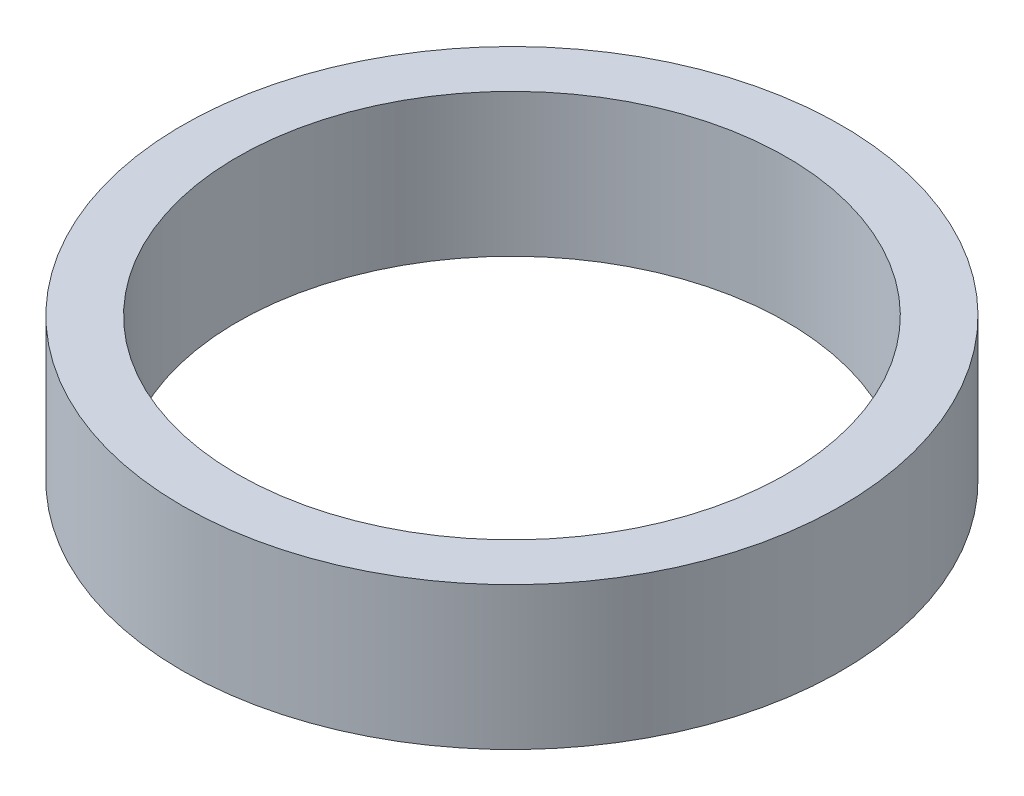
SolidWorks part; units mm, degrees
material "AISI 304"
ref_plane "前视基准面" through (0, 0, 0) normal (0, 0, 1) x (1, 0, 0)
ref_plane "上视基准面" through (0, 0, 0) normal (0, 1, 0) x (1, 0, 0)
ref_plane "右视基准面" through (0, 0, 0) normal (1, 0, 0) x (0, 0, -1)
sketch "Sketch1" plane through (0, 0, 0) normal (0, 1, 0) x (1, 0, 0)
  circle A0 centre (0, 0) radius 30
  circle A1 centre (0, 0) radius 25
  dimension "D1" = 50
  dimension "D2" = 60
extrude "Boss-Extrude1" add sketch "Sketch1" along normal mid plane 13
